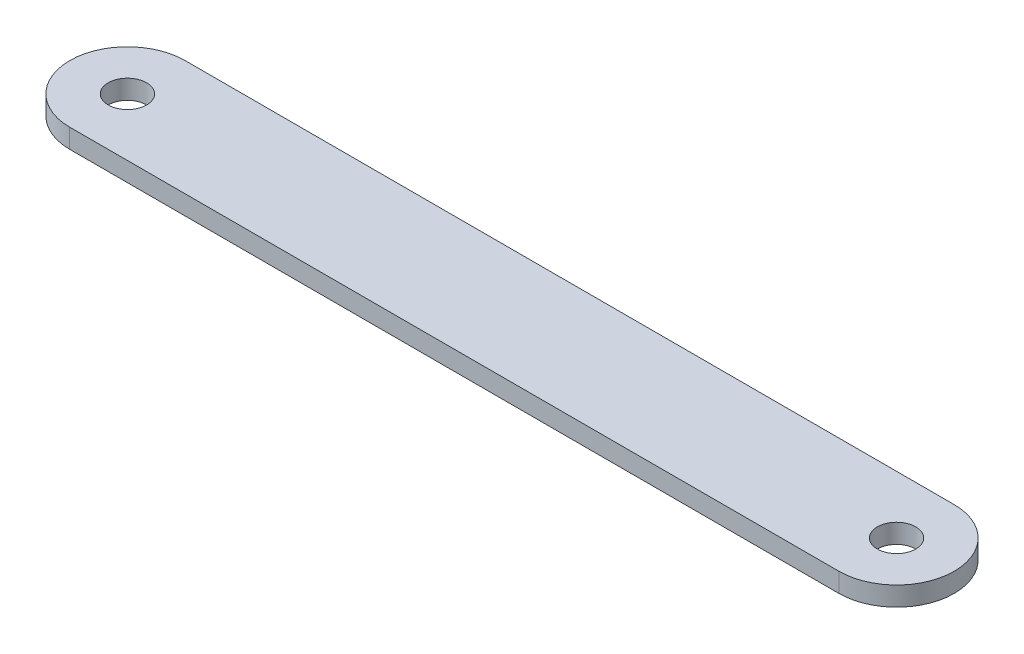
SolidWorks part; units mm, degrees
ref_plane "前视基准面" through (0, 0, 0) normal (0, 0, 1) x (1, 0, 0)
ref_plane "上视基准面" through (0, 0, 0) normal (0, 1, 0) x (1, 0, 0)
ref_plane "右视基准面" through (0, 0, 0) normal (1, 0, 0) x (0, 0, -1)
other "Configuration Table"
sketch "草图1" plane through (0, 0, 0) normal (0, 1, 0) x (1, 0, 0)
  line L0 (0, 0) -> (200, 0) construction
  line L1 (0, 15) -> (200, 15)
  line L2 (0, -15) -> (200, -15)
  arc A0 (0, 15) -> (0, -15) centre (0, 0) ccw
  arc A1 (200, -15) -> (200, 15) centre (200, 0) ccw
  circle A2 centre (0, 0) radius 5
  circle A3 centre (200, 0) radius 5
  point P3 (100, 0)
  dimension "D1" = 10
  dimension "D2" = 15
  dimension "D3" = 10
  dimension "D4" = 200
extrude "凸台-拉伸1" add sketch "草图1" along normal blind 5 contours L2 A1 L1 A0
